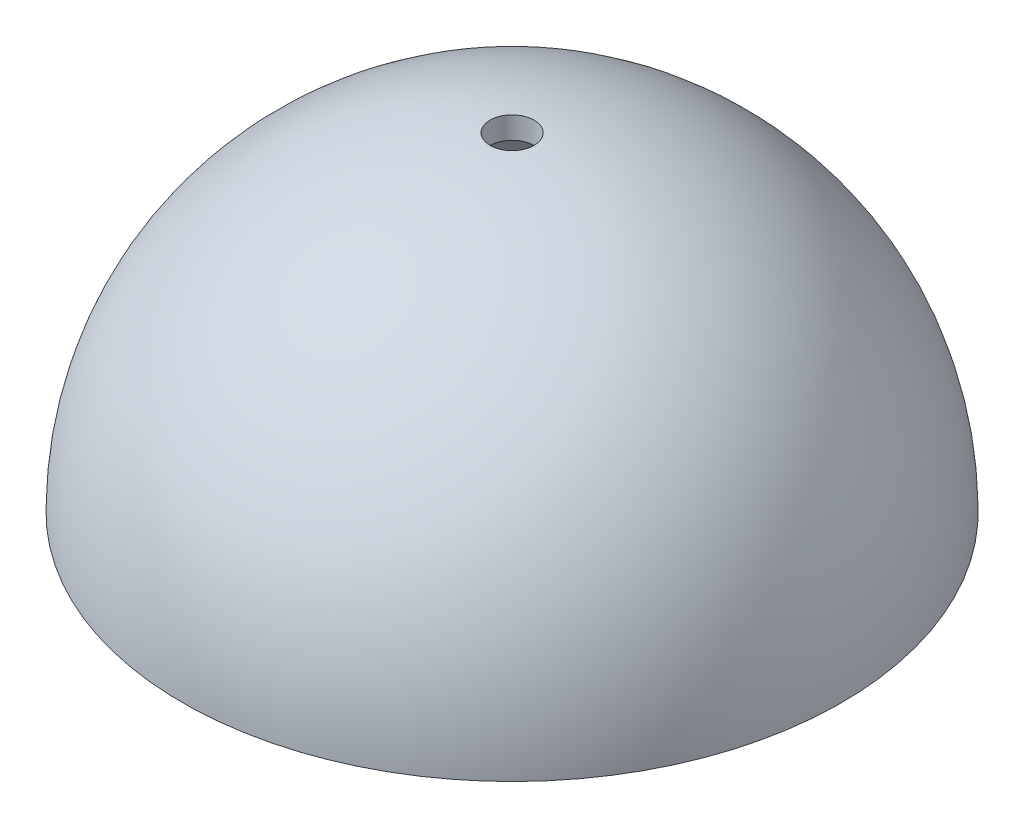
SolidWorks part; units mm, degrees
ref_plane "Front Plane" through (0, 0, 0) normal (0, 0, 1) x (1, 0, 0)
ref_plane "Top Plane" through (0, 0, 0) normal (0, 1, 0) x (1, 0, 0)
ref_plane "Right Plane" through (0, 0, 0) normal (1, 0, 0) x (0, 0, -1)
sketch "Sketch1" plane through (0, 0, 0) normal (0, 0, 1) x (1, 0, 0)
  line L0 (0, 0) -> (0, 150)
  line L1 (0, 0) -> (-150, 0)
  arc A0 (-150, 0) -> (0, 150) centre (0, 0) cw
  dimension "D1" = 150
revolve "Revolve1" add sketch "Sketch1" angle 360 about L0
shell "Shell1" thickness 10
sketch "Sketch2" plane through (0, 0, 0) normal (0, 1, 0) x (1, 0, 0)
  circle A0 centre (0, 0) radius 10
  dimension "D1" = 20
extrude "Cut-Extrude3" cut sketch "Sketch2" against normal through all and the other way through all
